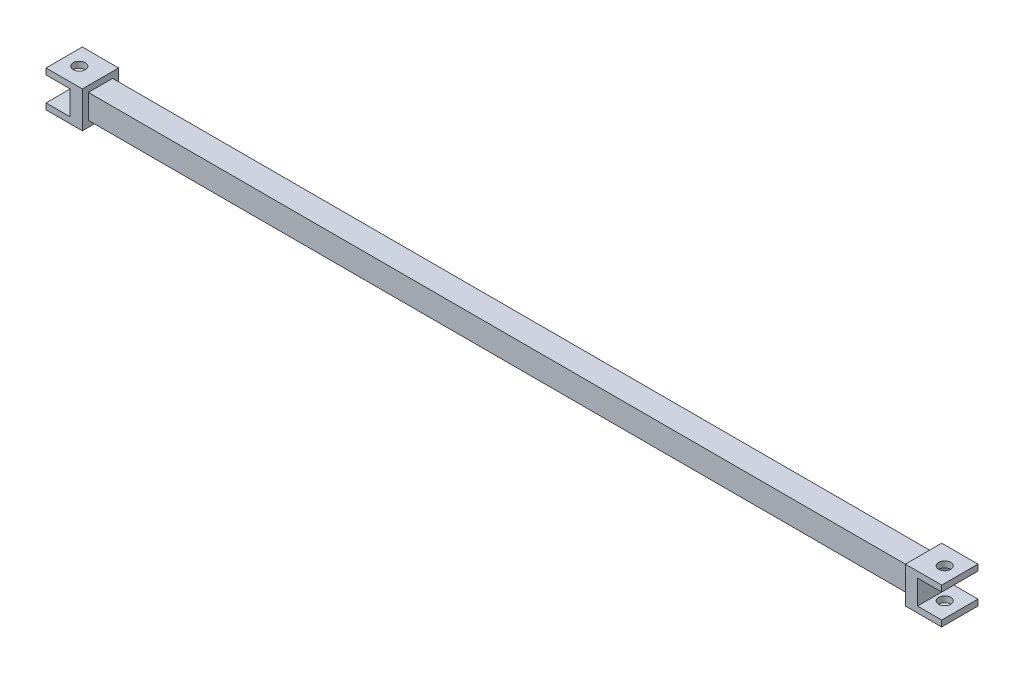
SolidWorks part; units mm, degrees
ref_plane "Ön Düzlem" through (0, 0, 0) normal (0, 0, 1) x (1, 0, 0)
ref_plane "Üst Düzlem" through (0, 0, 0) normal (0, 1, 0) x (1, 0, 0)
ref_plane "Sağ Düzlem" through (0, 0, 0) normal (1, 0, 0) x (0, 0, -1)
sketch "Çizim1" plane through (0, 0, 0) normal (0, 0, 1) x (1, 0, 0)
  line L1 (-34, 1) -> (34, 1)
  line L2 (-34, 1) -> (-34, -1)
  line L3 (-34, -1) -> (34, -1)
  line L4 (34, 1) -> (34, -1)
  line L5 (-34, 1) -> (34, -1) construction
  line L6 (-34, -1) -> (34, 1) construction
  point P0 (0, 0)
  dimension "D1" = 68
  dimension "D2" = 2
extrude "Yükseklik-Ekstrüzyon1" add sketch "Çizim1" along normal blind 2
sketch "Çizim2" plane through (-34, 0, 0) normal (-1, 0, 0) x (0, 0, 1)
  line L0 (2, 1) -> (2, -1) construction
  line L1 (2.5, -1.5) -> (-0.5, -1.5)
  line L2 (2.5, -1.5) -> (2.5, 1.5)
  line L3 (2.5, 1.5) -> (-0.5, 1.5)
  line L4 (-0.5, -1.5) -> (-0.5, 1.5)
  line L5 (2.5, -1.5) -> (-0.5, 1.5) construction
  line L6 (2.5, 1.5) -> (-0.5, -1.5) construction
  line L7 (2, -1) -> (0, -1) construction
  point P0 (1, 0)
  point P8 (2, 0)
  point P12 (1, -1)
  dimension "D2" = 3
  dimension "D1" = 3
extrude "Yükseklik-Ekstrüzyon2" add sketch "Çizim2" along normal blind 3
sketch "Çizim3" plane through (-37, 0, 0) normal (-1, 0, 0) x (0, 0, 1)
  line L0 (2.5, -1.5) -> (2.5, 1.5) construction
  line L1 (3.2458, -1) -> (-1.0747, -1)
  line L2 (3.2458, -1) -> (3.2458, 1)
  line L3 (3.2458, 1) -> (-1.0747, 1)
  line L4 (-1.0747, -1) -> (-1.0747, 1)
  line L5 (3.2458, -1) -> (-1.0747, 1) construction
  line L6 (3.2458, 1) -> (-1.0747, -1) construction
  point P0 (1.0856, 0)
  point P8 (2.5, 0)
  dimension "D1" = 2
extrude "Kes-Ekstrüzyon2" cut sketch "Çizim3" against normal blind 2
sketch "Çizim4" plane through (0, -1.5, 0) normal (0, -1, 0) x (1, 0, 0)
  line L0 (-37, -0.5) -> (-37, 2.5) construction
  circle A0 centre (-35.75, 1) radius 0.5
  dimension "D1" = 1
  dimension "D2" = 1.25
extrude "Kes-Ekstrüzyon3" cut sketch "Çizim4" against normal blind 4
mirror "Aynalama2" about plane through (0, 0, 0) normal (1, 0, 0) of "Kes-Ekstrüzyon3", "Kes-Ekstrüzyon2", "Yükseklik-Ekstrüzyon2"
